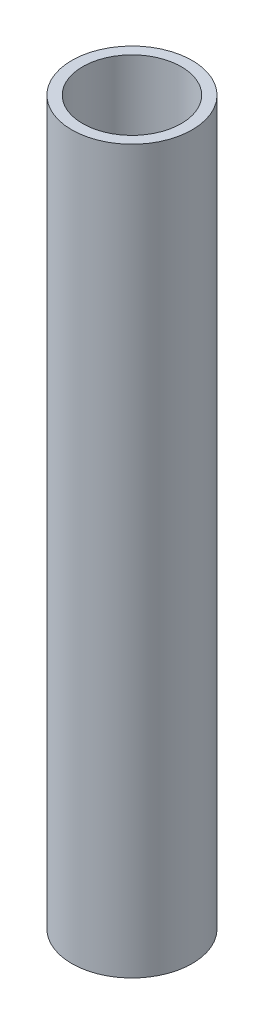
SolidWorks part; units mm, degrees
ref_plane "Front Plane" through (0, 0, 0) normal (0, 0, 1) x (1, 0, 0)
ref_plane "Top Plane" through (0, 0, 0) normal (0, 1, 0) x (1, 0, 0)
ref_plane "Right Plane" through (0, 0, 0) normal (1, 0, 0) x (0, 0, -1)
sketch "Sketch1" plane through (0, 0, 0) normal (0, 1, 0) x (1, 0, 0)
  circle A0 centre (0, 0) radius 12.7
  circle A1 centre (0, 0) radius 10.414
  dimension "D1" = 25.4
  dimension "D2" = 20.828
extrude "Boss-Extrude1" add sketch "Sketch1" along normal blind 152.4
